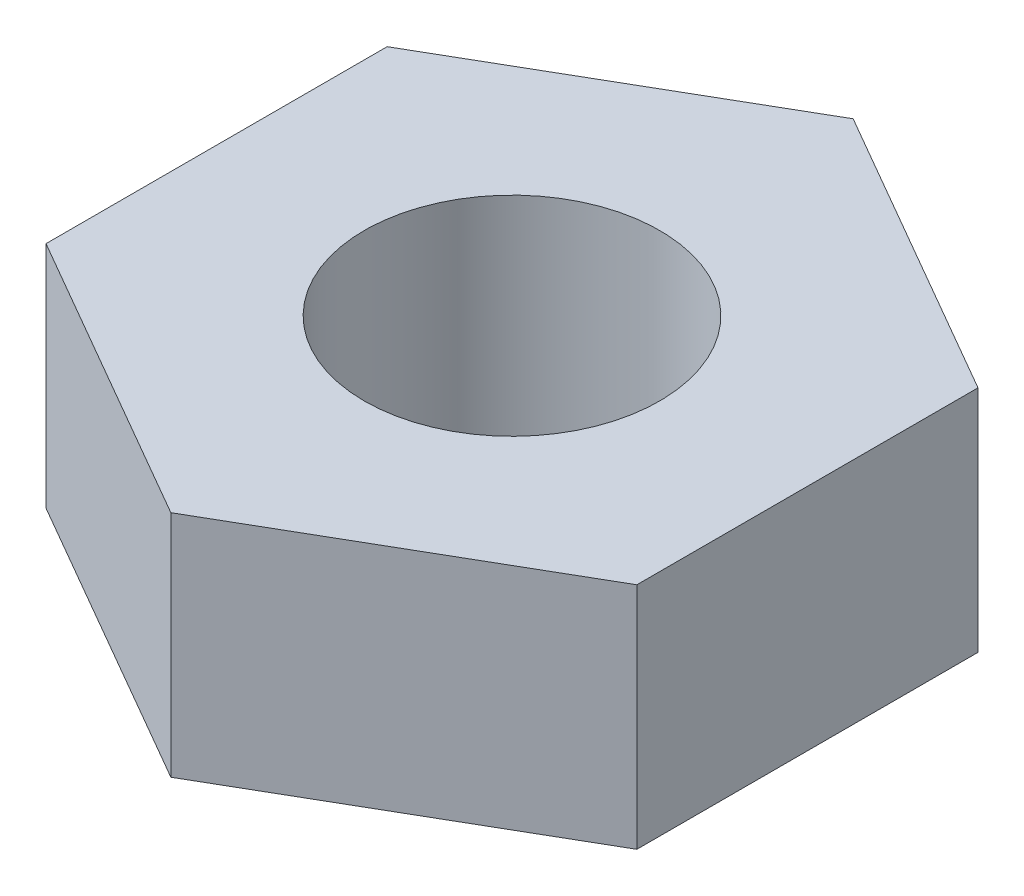
SolidWorks part; units mm, degrees
ref_plane "Front Plane" through (0, 0, 0) normal (0, 0, 1) x (1, 0, 0)
ref_plane "Top Plane" through (0, 0, 0) normal (0, 1, 0) x (1, 0, 0)
ref_plane "Right Plane" through (0, 0, 0) normal (1, 0, 0) x (0, 0, -1)
sketch "Sketch1" plane through (0, 0, 0) normal (0, 1, 0) x (1, 0, 0)
  line L1 (0, -2.829) -> (2.45, -1.4145)
  line L2 (2.45, -1.4145) -> (2.45, 1.4145)
  line L3 (2.45, 1.4145) -> (0, 2.829)
  line L4 (0, 2.829) -> (-2.45, 1.4145)
  line L5 (-2.45, 1.4145) -> (-2.45, -1.4145)
  line L6 (-2.45, -1.4145) -> (0, -2.829)
  circle A0 centre (0, 0) radius 2.45 construction
  circle A1 centre (0, 0) radius 1.225
  dimension "D1" = 2.45
  dimension "D2" = 4.9
extrude "Boss-Extrude1" add sketch "Sketch1" along normal blind 1.9
